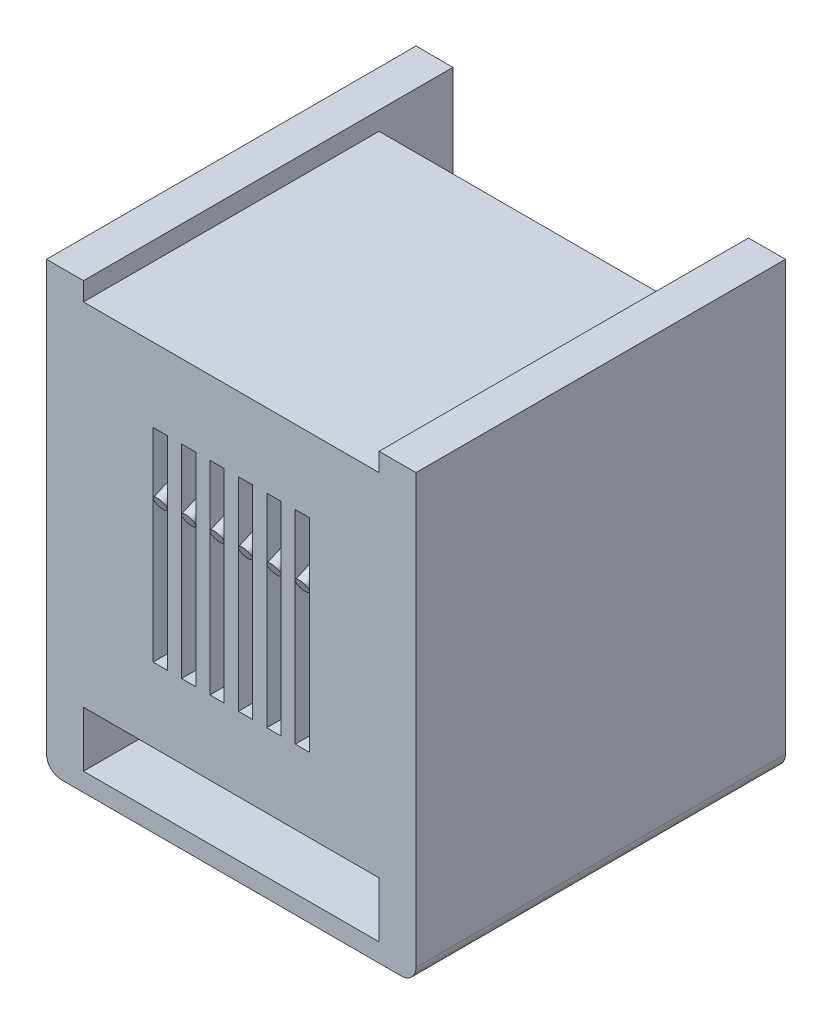
SolidWorks part; units mm, degrees
ref_plane "Front Plane" through (0, 0, 0) normal (0, 0, 1) x (1, 0, 0)
ref_plane "Top Plane" through (0, 0, 0) normal (0, 1, 0) x (1, 0, 0)
ref_plane "Right Plane" through (0, 0, 0) normal (1, 0, 0) x (0, 0, -1)
sketch "Sketch1" plane through (0, 0, 0) normal (0, 0, 1) x (1, 0, 0)
  line L0 (-5, 7.5) -> (-5, -5) construction
  line L1 (-6.25, 7.5) -> (6.25, 7.5) construction
  line L2 (-6.25, 7.5) -> (-6.25, -7.5)
  line L3 (-6.25, -7.5) -> (6.25, -7.5)
  line L4 (6.25, 7.5) -> (6.25, -7.5)
  line L5 (-5, -5) -> (-3.8125, -5) construction
  line L6 (-3.8125, -5) -> (-3.8125, -6.875) construction
  line L7 (-3.8125, -6.875) -> (-0.6875, -6.875) construction
  line L8 (-0.6875, -6.875) -> (-0.6875, -5) construction
  line L9 (-0.6875, -5) -> (0.5, -5) construction
  line L10 (0.5, -5) -> (0.5, -2.5) construction
  line L11 (0.5, -2.5) -> (5, -2.5) construction
  line L12 (5, -2.5) -> (5, 7.5)
  line L13 (5, -2.5) -> (6.25, -2.5) construction
  line L14 (-5, -5) -> (-6.25, -5) construction
  line L15 (5, 7.5) -> (6.25, 7.5)
  line L16 (-5, 7.5) -> (-6.25, 7.5)
  line L17 (5, -2.5) -> (5, -5)
  line L18 (5, -5) -> (3.8, -5)
  line L19 (3.8, -5) -> (3.8, -6.875)
  line L20 (3.8, -6.875) -> (0.7, -6.875)
  line L21 (0.7, -6.875) -> (0.7, -5)
  line L22 (0.7, -5) -> (-0.5, -5)
  line L23 (-0.5, -5) -> (-0.5, -2.5)
  line L24 (-0.5, -2.5) -> (-5, -2.5)
  line L25 (-5, 7.5) -> (-5, -2.5)
  point P4 (6.25, 0)
  point P5 (0, 7.5)
  dimension "D1" = 12.5
  dimension "D2" = 15
  dimension "D3" = 10
  dimension "D4" = 5
  dimension "D5" = 0.625
  dimension "D6" = 5.5
  dimension "D7" = 3.125
  dimension "D8" = 2.5
  dimension "D9" = 5.5
  dimension "D10" = 3.1
extrude "Extrude2" add sketch "Sketch1" along normal blind 12.5
sketch "Sketch2" plane through (0, 0, 12.5) normal (0, 0, 1) x (1, 0, 0)
  line L1 (-5, 6.875) -> (5, 6.875) construction
  line L2 (-5, 6.875) -> (-5, 4.375) construction
  line L3 (-5, 4.375) -> (5, 4.375) construction
  line L4 (5, 6.875) -> (5, 4.375)
  line L5 (5, 7.5) -> (5, -5) construction
  line L6 (-5, 4.375) -> (-3.125, 4.375)
  line L7 (-3.125, 4.375) -> (-3.125, 6.25)
  line L8 (-3.125, 6.25) -> (3.125, 6.25)
  line L9 (3.125, 6.25) -> (3.125, 4.375)
  line L10 (3.125, 4.375) -> (5, 4.375)
  line L12 (6.25, 7.5) -> (5, 7.5) construction
  line L13 (-0.5, -2.5) -> (-5, -2.5) construction
  line L14 (5, 6.875) -> (-5, 6.875)
  line L15 (-5, 6.875) -> (-5, 4.375)
  dimension "D1" = 1.875
  dimension "D2" = 6.875
  dimension "D3" = 0.625
  dimension "D4" = 0.625
extrude "Extrude3" add sketch "Sketch2" against normal offset from surface (10 mm away) 2.5 up to face at (0.5714, -1.6964, 0)
sketch "Sketch3" plane through (0, 6.25, 0) normal (0, -1, 0) x (1, 0, 0)
  line L0 (3.125, 2.5) -> (3.125, 12.5) construction
  line L1 (3.125, 5) -> (-3.125, 5) construction
  line L2 (3.125, 5) -> (3.125, 12.5)
  line L3 (-3.125, 12.5) -> (3.125, 12.5) construction
  line L4 (2.1635, 9.375) -> (2.1635, 5)
  line L5 (3.125, 12.5) -> (-3.125, 12.5)
  line L6 (3.125, 5) -> (2.6442, 5)
  line L7 (3.125, 2.5) -> (-3.125, 2.5) construction
  line L8 (-3.125, 2.5) -> (-3.125, 12.5) construction
  line L9 (2.6442, 5) -> (2.6442, 9.375)
  line L10 (2.6442, 9.375) -> (2.1635, 9.375)
  line L11 (2.1635, 5) -> (1.6827, 5)
  line L12 (1.6827, 5) -> (1.6827, 9.375)
  line L13 (-3.125, 12.5) -> (-3.125, 5)
  line L14 (1.6827, 9.375) -> (1.2019, 9.375)
  line L15 (1.2019, 9.375) -> (1.2019, 5)
  line L16 (1.2019, 5) -> (0.7212, 5)
  line L17 (0.7212, 5) -> (0.7212, 9.375)
  line L18 (0.7212, 9.375) -> (0.2404, 9.375)
  line L19 (0.2404, 9.375) -> (0.2404, 5)
  line L20 (0.2404, 5) -> (-0.2404, 5)
  line L21 (-0.2404, 5) -> (-0.2404, 9.375)
  line L22 (-0.2404, 9.375) -> (-0.7212, 9.375)
  line L23 (-0.7212, 9.375) -> (-0.7212, 5)
  line L24 (-0.7212, 5) -> (-1.2019, 5)
  line L25 (-1.2019, 5) -> (-1.2019, 9.375)
  line L26 (-1.2019, 9.375) -> (-1.6827, 9.375)
  line L27 (-1.6827, 9.375) -> (-1.6827, 5)
  line L28 (-1.6827, 5) -> (-2.1635, 5)
  line L29 (-2.1635, 5) -> (-2.1635, 9.375)
  line L30 (-2.1635, 9.375) -> (-2.6442, 9.375)
  line L31 (-2.6442, 9.375) -> (-2.6442, 5)
  line L32 (-2.6442, 5) -> (-3.125, 5)
  dimension "D1" = 2.5
  dimension "D3" = 4.375
extrude "Extrude4" add sketch "Sketch3" along normal up to surface (1.875 mm away) up to face at (4.0625, 4.375, 7.5)
sketch "Sketch4" plane through (0, 0, 12.5) normal (0, 0, 1) x (1, 0, 0)
  line L1 (-5, 6.875) -> (5, 6.875) construction
  line L2 (5, -5) -> (3.8, -5) construction
  line L3 (-5, -5) -> (5, -5)
  line L6 (2.1635, 4.375) -> (2.6442, 4.375) construction
  line L7 (1.2019, 4.375) -> (1.6827, 4.375) construction
  line L8 (0.2404, 4.375) -> (0.7212, 4.375) construction
  line L9 (-0.7212, 4.375) -> (-0.2404, 4.375) construction
  line L10 (-1.6827, 4.375) -> (-1.2019, 4.375) construction
  line L11 (-2.6442, 4.375) -> (-2.1635, 4.375) construction
  line L12 (2.1635, 4.375) -> (2.6442, 4.375) construction
  line L13 (1.2019, 4.375) -> (1.6827, 4.375) construction
  line L14 (0.2404, 4.375) -> (0.7212, 4.375) construction
  line L15 (-0.7212, 4.375) -> (-0.2404, 4.375) construction
  line L16 (-1.6827, 4.375) -> (-1.2019, 4.375) construction
  line L17 (-2.6442, 4.375) -> (-2.1635, 4.375) construction
  line L18 (5, -2.5) -> (-5, -2.5) construction
  line L19 (-2.6442, 4.375) -> (-2.6442, -2.5)
  line L20 (-2.6442, -2.5) -> (-2.1635, -2.5)
  line L21 (-2.1635, -2.5) -> (-2.1635, 4.375)
  line L22 (-2.1635, 4.375) -> (-1.6827, 4.375)
  line L23 (-1.6827, 4.375) -> (-1.6827, -2.5)
  line L24 (-1.6827, -2.5) -> (-1.2019, -2.5)
  line L25 (-1.2019, -2.5) -> (-1.2019, 4.375)
  line L26 (-1.2019, 4.375) -> (-0.7212, 4.375)
  line L27 (-0.7212, 4.375) -> (-0.7212, -2.5)
  line L28 (-0.7212, -2.5) -> (-0.2404, -2.5)
  line L29 (-0.2404, -2.5) -> (-0.2404, 4.375)
  line L30 (-0.2404, 4.375) -> (0.2404, 4.375)
  line L31 (0.2404, 4.375) -> (0.2404, -2.5)
  line L32 (0.2404, -2.5) -> (0.7212, -2.5)
  line L33 (0.7212, -2.5) -> (0.7212, 4.375)
  line L34 (0.7212, 4.375) -> (1.2019, 4.375)
  line L35 (1.2019, 4.375) -> (1.2019, -2.5)
  line L36 (1.2019, -2.5) -> (1.6827, -2.5)
  line L37 (1.6827, -2.5) -> (1.6827, 4.375)
  line L38 (1.6827, 4.375) -> (2.1635, 4.375)
  line L39 (2.1635, 4.375) -> (2.1635, -2.5)
  line L40 (2.1635, -2.5) -> (2.6442, -2.5)
  line L41 (2.6442, -2.5) -> (2.6442, 4.375)
  line L42 (-2.6442, 4.375) -> (-5, 4.375)
  line L43 (-5, 4.375) -> (-5, -5)
  line L44 (2.6442, 4.375) -> (5, 4.375)
  line L45 (5, 4.375) -> (5, -5)
extrude "Extrude5" add sketch "Sketch4" against normal blind 1.25
sketch "Sketch5" plane through (0, 0, 11.25) normal (0, 0, -1) x (-1, 0, 0)
  line L0 (-2.6442, 4.375) -> (-3.125, 4.375) construction
  line L1 (-1.6827, 4.375) -> (-2.1635, 4.375) construction
  line L2 (-0.7212, 4.375) -> (-1.2019, 4.375) construction
  line L3 (0.2404, 4.375) -> (-0.2404, 4.375) construction
  line L4 (1.2019, 4.375) -> (0.7212, 4.375) construction
  line L5 (2.1635, 4.375) -> (1.6827, 4.375) construction
  line L6 (3.125, 4.375) -> (2.6442, 4.375) construction
  line L7 (-2.6442, 4.375) -> (-3.125, 4.375) construction
  line L8 (-1.6827, 4.375) -> (-2.1635, 4.375) construction
  line L9 (-0.7212, 4.375) -> (-1.2019, 4.375) construction
  line L10 (0.2404, 4.375) -> (-0.2404, 4.375) construction
  line L11 (1.2019, 4.375) -> (0.7212, 4.375) construction
  line L12 (2.1635, 4.375) -> (1.6827, 4.375) construction
  line L13 (3.125, 4.375) -> (2.6442, 4.375) construction
  line L14 (-2.6442, 4.475) -> (-3.125, 4.475) construction
  line L15 (-1.6827, 4.475) -> (-2.1635, 4.475) construction
  line L16 (-0.7212, 4.475) -> (-1.2019, 4.475) construction
  line L17 (0.2404, 4.475) -> (-0.2404, 4.475) construction
  line L18 (1.2019, 4.475) -> (0.7212, 4.475) construction
  line L19 (2.1635, 4.475) -> (1.6827, 4.475) construction
  line L20 (3.125, 4.475) -> (2.6442, 4.475) construction
  line L21 (3.125, 0.9375) -> (-3.4027, 0.9375) construction
  line L23 (3.125, 4.475) -> (3.125, 0.9375)
  line L24 (2.6442, 4.375) -> (2.1635, 4.375)
  line L25 (3.125, 0.9375) -> (2.6442, 0.9375)
  line L26 (2.6442, 0.9375) -> (2.6442, 4.375)
  line L27 (2.1635, 4.375) -> (2.1635, 0.9375)
  line L28 (2.1635, 4.375) -> (2.1635, -2.5) construction
  line L29 (2.1635, 0.9375) -> (1.6827, 0.9375)
  line L30 (1.6827, 0.9375) -> (1.6827, 4.375)
  line L31 (1.6827, 4.375) -> (1.2019, 4.375)
  line L32 (1.2019, 4.375) -> (1.2019, 0.9375)
  line L33 (1.2019, 4.375) -> (1.2019, -2.5) construction
  line L34 (1.2019, 0.9375) -> (0.7212, 0.9375)
  line L35 (0.7212, 0.9375) -> (0.7212, 4.375)
  line L36 (0.7212, 4.375) -> (0.2404, 4.375)
  line L37 (0.2404, 0.9375) -> (-0.2404, 0.9375)
  line L38 (0.2404, 4.375) -> (0.2404, -2.5) construction
  line L39 (-0.2404, 0.9375) -> (-0.2404, 4.375)
  line L40 (-0.2404, 4.375) -> (-0.7212, 4.375)
  line L41 (-0.7212, 0.9375) -> (-1.2019, 0.9375)
  line L42 (-0.7212, 4.375) -> (-0.7212, -2.5) construction
  line L43 (-1.2019, 0.9375) -> (-1.2019, 4.375)
  line L44 (-1.2019, 4.375) -> (-1.6827, 4.375)
  line L45 (-1.6827, 4.375) -> (-1.6827, 0.9375)
  line L46 (-1.6827, 0.9375) -> (-2.1635, 0.9375)
  line L47 (-2.1635, 0.9375) -> (-2.1635, 4.375)
  line L48 (-2.1635, 4.375) -> (-2.6442, 4.375)
  line L50 (-0.2404, -2.5) -> (-0.2404, 4.375) construction
  line L51 (-1.2019, -2.5) -> (-1.2019, 4.375) construction
  line L52 (-0.7212, 4.375) -> (-0.7212, 0.9375)
  line L53 (0.2404, 4.375) -> (0.2404, 0.9375)
  line L54 (-2.6442, 4.375) -> (-2.6442, 0.9375)
  line L55 (-2.6442, 4.375) -> (-2.6442, -2.5) construction
  line L56 (-2.6442, 0.9375) -> (-3.125, 0.9375)
  line L57 (-3.125, 0.9375) -> (-3.125, 4.475)
  line L58 (-3.125, 4.475) -> (3.125, 4.475)
  dimension "D1" = 0.1
extrude "Extrude6" add sketch "Sketch5" along normal blind 0.625
sketch "Sketch6" plane through (0, 0, 12.5) normal (0, 0, 1) x (1, 0, 0)
  line L1 (-5, -6.875) -> (5, -6.875)
  line L2 (-5, -6.875) -> (-5, -5)
  line L3 (-5, -5) -> (5, -5)
  line L4 (5, -6.875) -> (5, -5)
  line L5 (5, 7.5) -> (5, -5) construction
  line L6 (0.7, -5) -> (3.8, -5) construction
  line L8 (-5, 6.875) -> (-5, 7.5) construction
  line L9 (3.8, -6.875) -> (0.7, -6.875) construction
extrude "Cut-Extrude1" cut sketch "Sketch6" against normal offset from surface (10 mm away) 2.5 up to face at (0.5714, -1.6964, 0)
sketch "Sketch7" plane through (0, 0, 11.25) normal (0, 0, -1) x (-1, 0, 0)
  line L5 (5, -2.5) -> (4.4, -2.5)
  line L6 (5, -2.5) -> (5, -2)
  line L7 (5, -2) -> (4.4, -2)
  line L8 (4.4, -2.5) -> (4.4, -2)
  dimension "D3" = 0.5
  dimension "D4" = 0.6
extrude "Extrude7" add sketch "Sketch7" along normal blind 1.25
sketch "Sketch8" plane through (0, 0, 9.375) normal (0, 0, -1) x (-1, 0, 0)
  line L0 (-3.125, 6.25) -> (3.125, 6.25) construction
  line L1 (-2.1635, 4.375) -> (-2.1635, 6.25) construction
  line L2 (-2.6442, 4.375) -> (-2.6442, 6.25) construction
  line L3 (-2.4038, 6.0096) -> (2.4038, 6.0096) construction
  line L8 (-0.7212, 4.375) -> (-0.7212, 6.25) construction
  line L9 (0.2404, 4.375) -> (0.2404, 6.25) construction
  line L10 (1.2019, 4.375) -> (1.2019, 6.25) construction
  line L11 (2.1635, 4.375) -> (2.1635, 6.25) construction
  line L12 (-1.2019, 4.375) -> (-1.2019, 6.25) construction
  circle A0 centre (-2.4038, 6.0096) radius 0.2404 construction
  circle A1 centre (-1.4423, 6.0096) radius 0.2404 construction
  circle A2 centre (-0.4808, 6.0096) radius 0.2404 construction
  circle A3 centre (0.4808, 6.0096) radius 0.2404 construction
  circle A4 centre (1.4423, 6.0096) radius 0.2404 construction
  circle A5 centre (2.4038, 6.0096) radius 0.2404 construction
  circle A6 centre (2.4038, 6.0096) radius 0.2254
  circle A7 centre (1.4423, 6.0096) radius 0.2254
  circle A8 centre (0.4808, 6.0096) radius 0.2254
  circle A9 centre (-0.4808, 6.0096) radius 0.2254
  circle A10 centre (-1.4423, 6.0096) radius 0.2254
  circle A11 centre (-2.4038, 6.0096) radius 0.2254
  dimension "D1" = 0.015
sketch "Sketch9" plane through (0, 0, 0) normal (1, 0, 0) x (0, 0, -1)
  line L0 (-9.375, 6.0096) -> (-6.279, 6.0096)
  line L1 (-9.375, 5.7692) -> (-9.375, 6.25) construction
  line L2 (-6.0796, 5.0511) -> (-12.5, 2.2596)
  line L3 (-12.5, 4.375) -> (-12.5, -2.5) construction
  arc A0 (-6.279, 6.0096) -> (-6.0796, 5.0511) centre (-6.279, 5.5096) cw
  point P9 (-3.875, 6.0096)
  dimension "D3" = 0.5
  dimension "D1" = 3.75
  dimension "D2" = 5.5
sweep "Sweep1" add profiles "Sketch8" path "Sketch9"
fillet "Fillet1" radius 0.5 2 edges at (6.25, -7.5, 6.25) (-6.25, -7.5, 6.25)
